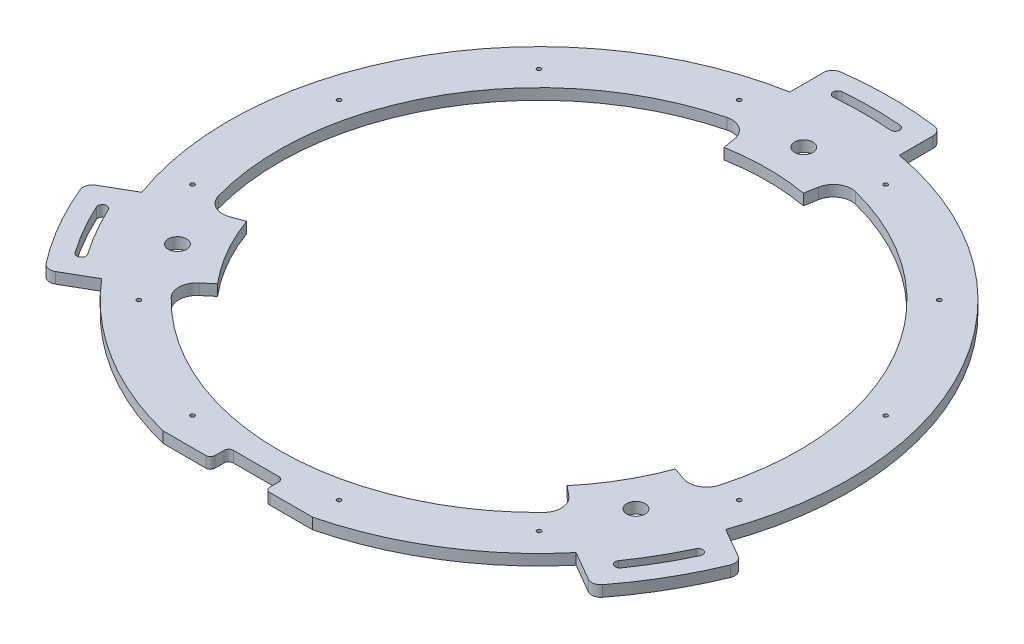
SolidWorks part; units mm, degrees
ref_plane "Front Plane" through (0, 0, 0) normal (0, 0, 1) x (1, 0, 0)
ref_plane "Top Plane" through (0, 0, 0) normal (0, 1, 0) x (1, 0, 0)
ref_plane "Right Plane" through (0, 0, 0) normal (1, 0, 0) x (0, 0, -1)
sketch "Sketch1" plane through (0, 0, 0) normal (0, 1, 0) x (1, 0, 0)
  circle A0 centre (0, 0) radius 250
  circle A1 centre (0, 0) radius 340
  circle A3 centre (0, 0) radius 340 construction
  dimension "D1" = 500
extrude "Boss-Extrude1" add sketch "Sketch1" along normal blind 12
sketch "Sketch2" plane through (0, 0, 0) normal (0, -1, 0) x (1, 0, 0)
  line L0 (0, 0) -> (549.798, 317.426) construction
  line L1 (0, 0) -> (604.1918, 0) construction
  line L2 (351.8598, 133.8643) -> (319.8275, 115.3705)
  line L3 (291.8598, 237.7874) -> (259.8275, 219.2935)
  line L4 (298.9905, 209.3554) -> (290.799, 203.6196) construction
  arc A0 (304.7761, 235.2372) -> (356.1094, 146.3252) centre (0, 0) cw
  circle A1 centre (0, 0) radius 340 construction
  arc A2 (291.8598, 237.7874) -> (304.7761, 235.2372) centre (296.8598, 229.1271) cw
  arc A3 (356.1094, 146.3252) -> (351.8598, 133.8643) centre (346.8598, 142.5246) cw
  arc A4 (298.9905, 209.3554) -> (330.8023, 154.2557) centre (0, 0) cw
  arc A5 (321.7393, 150.0295) -> (290.799, 203.6196) centre (0, 0) ccw
  arc A6 (298.9905, 209.3554) -> (290.799, 203.6196) centre (294.8947, 206.4875) ccw
  arc A7 (330.8023, 154.2557) -> (321.7393, 150.0295) centre (326.2708, 152.1426) cw
  arc A29 (319.8275, 115.3705) -> (259.8275, 219.2935) centre (0, 0) ccw
  point P12 (299.3459, 242.1095)
  point P15 (359.3459, 138.1864)
  dimension "D2" = 10
  dimension "D3" = 10
  dimension "D4" = 360
  dimension "D5" = 385
  dimension "D1" = 30
  dimension "D6" = 60
  dimension "D7" = 5
extrude "Boss-Extrude2" add sketch "Sketch2" against normal blind 12
pattern_circular "CirPattern1" count 3 over 360 about axis through (0, 0, 0) along (0, 1, 0) of "Boss-Extrude2"
sketch "Sketch6" plane through (0, 12, 0) normal (0, 1, 0) x (1, 0, 0)
  line L4 (248.3083, -90.3768) -> (234.9232, -85.505) construction
  line L5 (43.412, 246.2019) -> (0, 0) construction
  line L13 (248.3083, -90.3768) -> (234.9232, -85.505)
  line L16 (0, 0) -> (234.9232, -85.505) construction
  line L17 (43.412, 246.2019) -> (45.8855, 260.2297)
  line L18 (-226.3788, -253.6782) -> (-48.5351, -412.3834)
  line L19 (-226.3788, -253.6782) -> (-48.5351, -412.3834)
  line L20 (-28.5605, -420) -> (28.5605, -420)
  line L21 (-28.5605, -420) -> (28.5605, -420)
  line L22 (48.5351, -412.3834) -> (226.3788, -253.6782)
  line L23 (48.5351, -412.3834) -> (226.3788, -253.6782)
  arc A5 (70.5312, 276.1346) -> (45.8855, 260.2297) centre (65.5817, 256.7568) ccw construction
  arc A6 (248.3083, -90.3768) -> (274.4052, -76.9855) centre (255.1487, -71.583) ccw
  arc A7 (274.4052, -76.9855) -> (70.5312, 276.1346) centre (0, 0) ccw
  arc A8 (70.5312, 276.1346) -> (45.8855, 260.2297) centre (65.5817, 256.7568) ccw
  arc A9 (43.412, 246.2019) -> (234.9232, -85.505) centre (0, 0) cw
  arc A24 (28.5605, -420) -> (48.5351, -412.3834) centre (28.5605, -390) ccw
  arc A33 (226.3788, -253.6782) -> (-226.3788, -253.6782) centre (0, 0) ccw
  arc A34 (226.3788, -253.6782) -> (-226.3788, -253.6782) centre (0, 0) ccw
  arc A35 (28.5605, -420) -> (48.5351, -412.3834) centre (28.5605, -390) ccw
  arc A36 (-48.5351, -412.3834) -> (-28.5605, -420) centre (-28.5605, -390) ccw
  arc A37 (-48.5351, -412.3834) -> (-28.5605, -420) centre (-28.5605, -390) ccw
  dimension "D3" = 100
  dimension "D2" = 0
extrude "Cut-Extrude1" cut sketch "Sketch6" against normal blind 12
pattern_circular "CirPattern2" count 3 over 360 about axis through (0, 0, 0) along (0, 1, 0) of "Cut-Extrude1"
sketch "Sketch7" plane through (0, 0, 0) normal (0, -1, 0) x (1, 0, 0)
  line L0 (-81.8535, 330) -> (81.8535, 330)
  arc A0 (259.8275, 219.2935) -> (-259.8275, 219.2935) centre (0, 0) ccw construction
  arc A1 (81.8535, 330) -> (-81.8535, 330) centre (0, 0) ccw
  dimension "D1" = 330
extrude "Cut-Extrude2" cut sketch "Sketch7" against normal blind 12
sketch "Sketch8" plane through (0, 12, 0) normal (0, 1, 0) x (1, 0, 0)
  line L0 (0, 0) -> (0, 290) construction
  circle A0 centre (0, 290) radius 10
  circle A1 centre (251.1474, -145) radius 10
  circle A2 centre (-251.1474, -145) radius 10
  circle A3 centre (0, 0) radius 340 construction
  point P10 (0, 0)
  dimension "D1" = 20
  dimension "D2" = 290
  dimension "D3" = 3
extrude "Cut-Extrude3" cut sketch "Sketch8" against normal blind 12
sketch "Sketch9" plane through (0, 12, 0) normal (0, 1, 0) x (1, 0, 0)
  line L0 (0, 0) -> (0, -330) construction
  line L1 (-81.8535, -330) -> (81.8535, -330) construction
  line L2 (30, -330) -> (30, -310)
  line L3 (30, -310) -> (-30, -310)
  line L4 (-30, -330) -> (-30, -310)
  line L5 (-30, -330) -> (30, -330)
  point P9 (0, -310)
  dimension "D1" = 60
  dimension "D2" = 310
extrude "Cut-Extrude4" cut sketch "Sketch9" against normal blind 12
fillet "Fillet1" radius 5 4 edges at (30, 6, 330) (30, 6, 310) (-30, 6, 310) (-30, 6, 330)
hole_wizard "CSK for M4 Flat Head Machine Screw" positions "Sketch10" profile "Sketch11" countersink size "M4" standard "ANSI Metric" end condition through all
sketch "Sketch10" plane through (0, 48, 0) normal (0, 1, 0) x (1, 0, 0)
  line L0 (80.2339, 299.437) -> (0, 0) construction
  line L2 (0, 0) -> (0, 423.7069) construction
  circle A0 centre (0, 0) radius 310 construction
  point P0 (80.2339, 299.437)
  point P21 (219.2031, 219.2031)
  point P22 (299.437, 80.2339)
  point P23 (299.437, -80.2339)
  point P24 (219.2031, -219.2031)
  point P25 (80.2339, -299.437)
  point P26 (-80.2339, -299.437)
  point P27 (-219.2031, -219.2031)
  point P28 (-299.437, -80.2339)
  point P29 (-299.437, 80.2339)
  point P30 (-219.2031, 219.2031)
  point P31 (-80.2339, 299.437)
  point P32 (0, 0)
sketch "Sketch11" plane through (80.2339, 48, -299.437) normal (1, 0, 0) x (0, 0, 1)
  line L0 (0, 0) -> (0, 48)
  line L1 (0, 48) -> (2.25, 48)
  line L2 (2.25, 48) -> (2.25, 2.45)
  line L3 (2.25, 2.45) -> (4.7, 0)
  line L4 (4.7, 0) -> (0, 0)
  line L5 (-2.25, 2.45) -> (-4.7, 0) construction
  line L6 (0, -6.35) -> (0, 107.95) construction
  dimension "Thru Hole Dia." = 4.5
  dimension "Thru Hole Depth" = 48
  dimension "Near C'Sink Dia." = 9.4
  dimension "Near C'Sink Angle" = 90
sketch "Sketch12" plane through (0, 12, 0) normal (0, 1, 0) x (1, 0, 0)
  line L0 (0, 0) -> (-321.3938, -383.0222)
  line L1 (0, 0) -> (-171.0101, 469.8463)
  line L2 (0, 0) -> (0, -492.5115) construction
  arc A0 (-171.0101, 469.8463) -> (-321.3938, -383.0222) centre (0, 0) ccw
  dimension "D2" = 500
  dimension "D1" = 120
  dimension "D3" = 40
extrude "Cut-Extrude5" [suppressed] cut sketch "Sketch12" against normal blind 12 flip side to cut
sketch "Sketch13" plane through (0, 12, 0) normal (0, 1, 0) x (1, 0, 0)
  line L0 (0, 0) -> (-171.0101, 469.8463)
  line L1 (0, 0) -> (492.4039, -86.8241)
  line L2 (0, 0) -> (0, -510.7092) construction
  arc A0 (-171.0101, 469.8463) -> (492.4039, -86.8241) centre (0, 0) cw
  dimension "D3" = 500
  dimension "D1" = 160
  dimension "D2" = 120
extrude "Cut-Extrude6" [suppressed] cut sketch "Sketch13" against normal blind 12 flip side to cut
sketch "Sketch14" plane through (0, 12, 0) normal (0, 1, 0) x (1, 0, 0)
  line L0 (0, 0) -> (-321.3938, -383.0222)
  line L1 (0, 0) -> (492.4039, -86.8241)
  line L2 (0, 0) -> (0, -470.846) construction
  arc A0 (492.4039, -86.8241) -> (-321.3938, -383.0222) centre (0, 0) cw
  dimension "D1" = 120
  dimension "D2" = 500
  dimension "D3" = 40
extrude "Cut-Extrude7" [suppressed] cut sketch "Sketch14" against normal blind 12 flip side to cut
